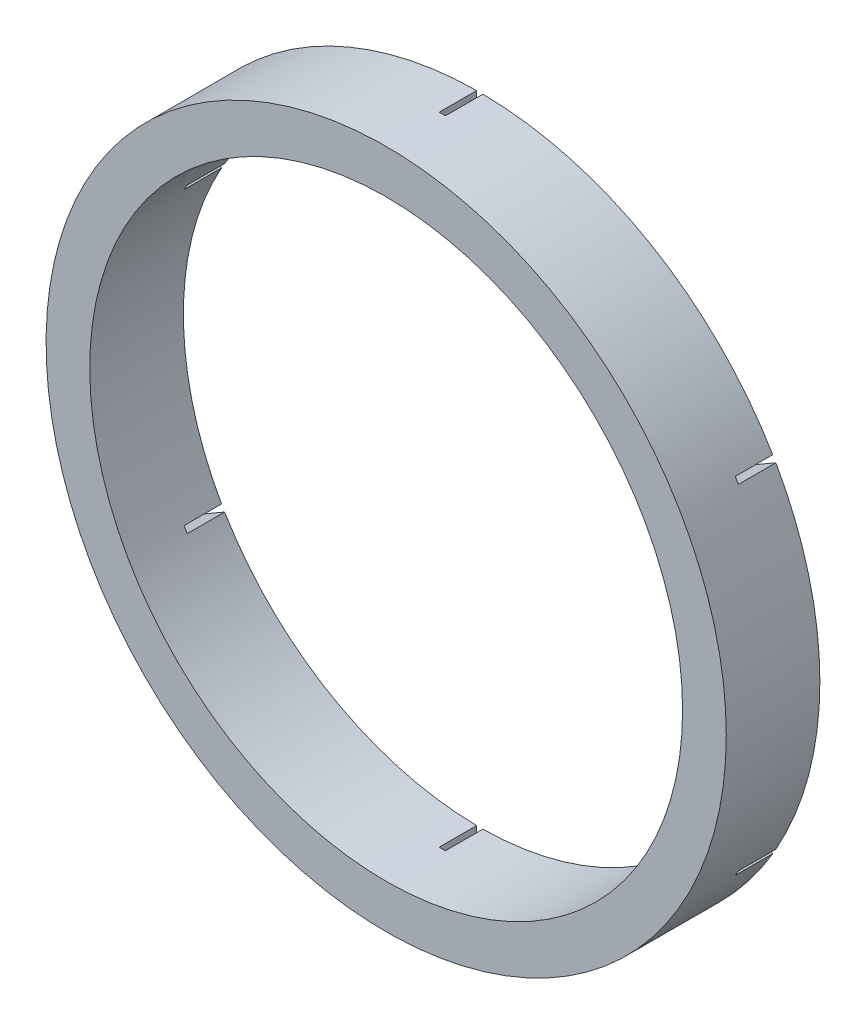
SolidWorks part; units mm, degrees
ref_plane "Face" through (0, 0, 0) normal (0, 0, 1) x (1, 0, 0)
ref_plane "Dessus" through (0, 0, 0) normal (0, 1, 0) x (1, 0, 0)
ref_plane "Droite" through (0, 0, 0) normal (1, 0, 0) x (0, 0, -1)
sketch "Esquisse1" plane through (0, 0, 0) normal (0, 0, 1) x (1, 0, 0)
  circle A0 centre (0, 0) radius 54.5
  circle A1 centre (0, 0) radius 47.5
  dimension "D1" = 95
  dimension "D2" = 109
extrude "Boss.-Extru.1" add sketch "Esquisse1" along normal blind 15
sketch "Esquisse2" plane through (0, 0, 0) normal (0, 0, -1) x (-1, 0, 0)
  line L0 (48.966, 27.6932) -> (40.0941, 22.571)
  line L1 (-0.5, 46.008) -> (0.5, 46.008)
  line L2 (-0.5, 46.008) -> (-0.5, 56.2524)
  line L3 (-0.5, 56.2524) -> (0.5, 56.2524)
  line L4 (0.5, 56.2524) -> (0.5, 46.008)
  line L5 (39.5941, 23.437) -> (48.466, 28.5592)
  line L6 (48.466, 28.5592) -> (48.966, 27.6932)
  line L7 (39.5941, 23.437) -> (40.0941, 22.571)
  line L8 (48.466, -28.5592) -> (39.5941, -23.437)
  line L9 (40.0941, -22.571) -> (48.966, -27.6932)
  line L10 (48.966, -27.6932) -> (48.466, -28.5592)
  line L11 (40.0941, -22.571) -> (39.5941, -23.437)
  line L12 (-0.5, -56.2524) -> (-0.5, -46.008)
  line L13 (0.5, -46.008) -> (0.5, -56.2524)
  line L14 (0.5, -56.2524) -> (-0.5, -56.2524)
  line L15 (0.5, -46.008) -> (-0.5, -46.008)
  line L16 (-48.966, -27.6932) -> (-40.0941, -22.571)
  line L17 (-39.5941, -23.437) -> (-48.466, -28.5592)
  line L18 (-48.466, -28.5592) -> (-48.966, -27.6932)
  line L19 (-39.5941, -23.437) -> (-40.0941, -22.571)
  line L20 (-48.466, 28.5592) -> (-39.5941, 23.437)
  line L21 (-40.0941, 22.571) -> (-48.966, 27.6932)
  line L22 (-48.966, 27.6932) -> (-48.466, 28.5592)
  line L23 (-40.0941, 22.571) -> (-39.5941, 23.437)
  point P27 (0, 0)
  point P46 (0, 0)
  dimension "D1" = 6
extrude "Enlèv. mat.-Extru.1" cut sketch "Esquisse2" against normal blind 6
